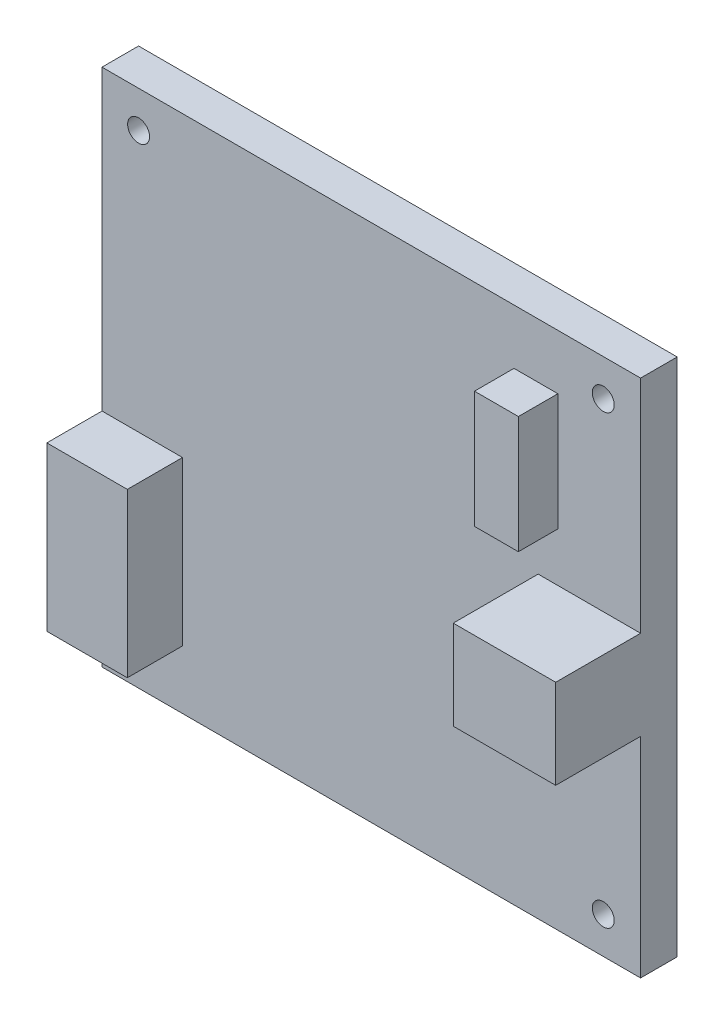
SolidWorks part; units mm, degrees
material "PCB"
ref_plane "Front Plane" through (0, 0, 0) normal (0, 0, 1) x (1, 0, 0)
ref_plane "Top Plane" through (0, 0, 0) normal (0, 1, 0) x (1, 0, 0)
ref_plane "Right Plane" through (0, 0, 0) normal (1, 0, 0) x (0, 0, -1)
sketch "Sketch1" plane through (0, 0, 0) normal (0, 0, 1) x (1, 0, 0)
  line L1 (0, 0) -> (73.6, 0)
  line L2 (0, 0) -> (0, 71)
  line L3 (0, 71) -> (73.6, 71)
  line L4 (73.6, 0) -> (73.6, 71)
  dimension "D1" = 73.6
  dimension "D2" = 71
extrude "Boss-Extrude1" add sketch "Sketch1" along normal blind 5
sketch "Sketch2" plane through (0, 0, 5) normal (0, 0, 1) x (1, 0, 0)
  line L0 (0, 0) -> (73.6, 0) construction
  line L1 (0, 71) -> (0, 0) construction
  circle A0 centre (5, 5) radius 1.5
  circle A1 centre (68.5, 5) radius 1.5
  circle A2 centre (68.5, 66) radius 1.5
  circle A3 centre (5, 66) radius 1.5
  dimension "D3" = 3
  dimension "D1" = 63.5
  dimension "D2" = 61
  dimension "D4" = 5
  dimension "D5" = 5
extrude "Cut-Extrude1" cut sketch "Sketch2" against normal through all
sketch "Sketch3" plane through (0, 0, 5) normal (0, 0, 1) x (1, 0, 0)
  line L0 (0, 71) -> (0, 0) construction
  line L1 (0, 8) -> (11, 8)
  line L2 (0, 8) -> (0, 30.3)
  line L3 (0, 30.3) -> (11, 30.3)
  line L4 (11, 8) -> (11, 30.3)
  line L5 (0, 0) -> (73.6, 0) construction
  dimension "D1" = 8
  dimension "D2" = 22.3
  dimension "D3" = 11
extrude "Boss-Extrude2" add sketch "Sketch3" along normal blind 7.54
sketch "Sketch4" plane through (0, 0, 5) normal (0, 0, 1) x (1, 0, 0)
  line L0 (73.6, 0) -> (73.6, 71) construction
  line L1 (73.6, 40.8) -> (59.6, 40.8)
  line L2 (73.6, 40.8) -> (73.6, 28.6)
  line L3 (73.6, 28.6) -> (59.6, 28.6)
  line L4 (59.6, 40.8) -> (59.6, 28.6)
  line L5 (0, 0) -> (73.6, 0) construction
  dimension "D1" = 28.6
  dimension "D2" = 12.2
  dimension "D3" = 14
extrude "Boss-Extrude3" add sketch "Sketch4" along normal blind 11.6
sketch "Sketch5" plane through (0, 0, 5) normal (0, 0, 1) x (1, 0, 0)
  line L0 (0, 0) -> (73.6, 0) construction
  line L1 (56.3, 63.5) -> (62.3, 63.5)
  line L2 (56.3, 63.5) -> (56.3, 47.5)
  line L3 (56.3, 47.5) -> (62.3, 47.5)
  line L4 (62.3, 63.5) -> (62.3, 47.5)
  line L5 (73.6, 40.8) -> (73.6, 71) construction
  dimension "D1" = 47.5
  dimension "D2" = 11.3
  dimension "D3" = 6
  dimension "D4" = 16
extrude "Boss-Extrude4" add sketch "Sketch5" along normal blind 5.4
